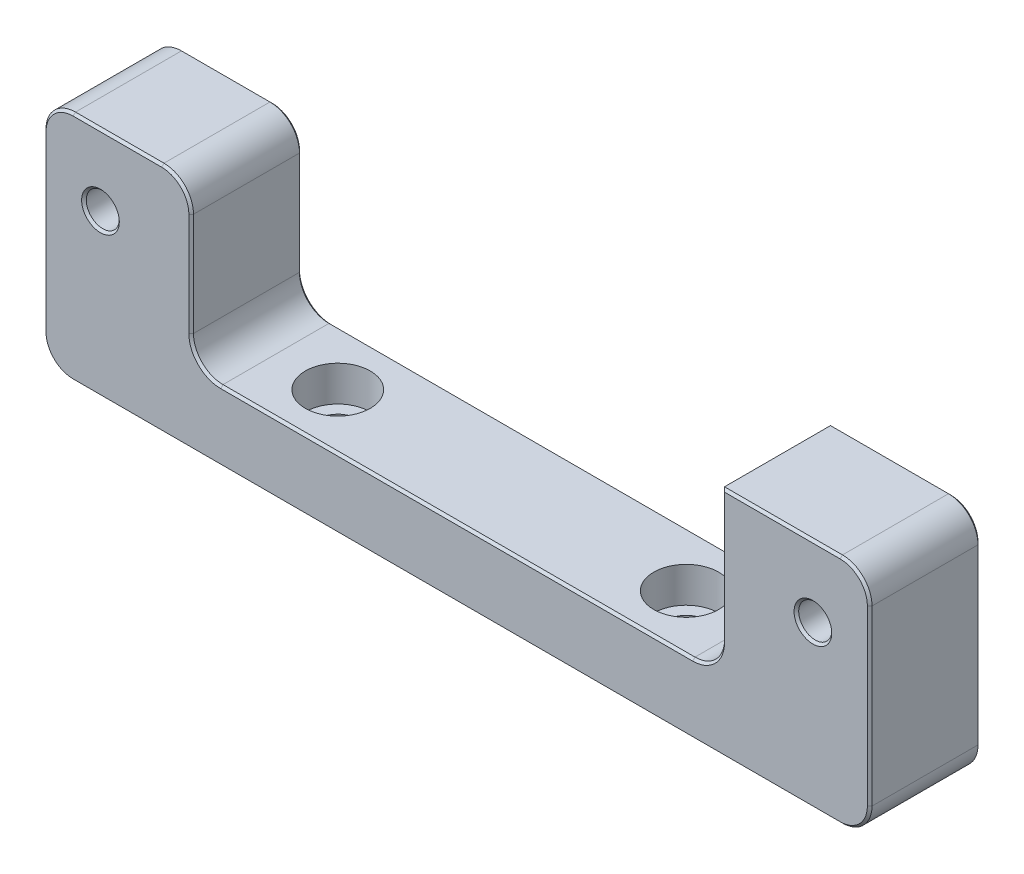
SolidWorks part; units mm, degrees
material "PEEK"
ref_plane "Front" through (0, 0, 0) normal (0, 0, 1) x (1, 0, 0)
ref_plane "Top" through (0, 0, 0) normal (0, 1, 0) x (1, 0, 0)
ref_plane "Right" through (0, 0, 0) normal (1, 0, 0) x (0, 0, -1)
sketch "Sketch1" plane through (0, 0, 0) normal (0, 0, 1) x (1, 0, 0)
  line L1 (0, 0) -> (-71.12, 0)
  line L2 (0, 0) -> (0, 20)
  line L3 (0, 20) -> (-71.12, 20)
  line L4 (-71.12, 0) -> (-71.12, 20)
  dimension "D1" = 71.12
  dimension "D2" = 20
extrude "Extrude1" add sketch "Sketch1" along normal blind 9.525
sketch "Sketch2" plane through (0, 0, 9.525) normal (0, 0, 1) x (1, 0, 0)
  line L0 (0, 20) -> (-71.12, 20) construction
  line L1 (-58.42, 20) -> (-12.7, 20)
  line L2 (-58.42, 20) -> (-58.42, 6.03)
  line L3 (-58.42, 6.03) -> (-12.7, 6.03)
  line L4 (-12.7, 20) -> (-12.7, 6.03)
  line L5 (0, 0) -> (0, 20) construction
  dimension "D1" = 13.97
  dimension "D2" = 45.72
  dimension "D3" = 12.7
extrude "Extrude2" cut sketch "Sketch2" against normal through all
ref_plane "Plane1" through (0, 0, 4.7625) normal (0, 0, -1) x (-1, 0, 0)
ref_plane "Plane2" through (-35.56, 0, 0) normal (-1, 0, 0) x (0, 0, 1)
hole_wizard "Hole1" positions "3DSketch1" profile "Sketch3" legacy end condition through all
sketch3d "3DSketch1"
  point P0 (-50.56, 6.03, 4.7625)
  point P2 (-20.56, 6.03, 4.7625)
  dimension "D1" = 15
  dimension "D2" = 15
sketch "Sketch3" plane through (-50.56, 6.03, 4.7625) normal (1, 0, 0) x (0, 0, 1)
  line L0 (0, 0) -> (0, 6.03)
  line L1 (0, 6.03) -> (1.7272, 6.03)
  line L3 (1.7272, 6.03) -> (1.7272, 3.048)
  line L4 (1.7272, 3.048) -> (2.794, 3.048)
  line L5 (2.794, 3.048) -> (2.794, 0)
  line L7 (2.794, 0) -> (0, 0)
  line L11 (0, -6.35) -> (0, 107.95) construction
  dimension "Thru Hole Dia." = 3.4544
  dimension "Thru Hole Depth" = 6.03
  dimension "C'Bore Dia." = 5.588
  dimension "C'Bore Depth" = 3.048
hole_wizard "#4-40 Tapped Hole1" positions "3DSketch2" profile "Sketch4" tap size "#4-40" standard "Ansi Inch"
sketch3d "3DSketch2"
  line L0 (-58.42, 20, 9.525) -> (-71.12, 20, 9.525) construction
  point P0 (-66.2305, 13.9, 9.525)
  point P2 (-4.8895, 13.9, 9.525)
  dimension "D1" = 6.1
  dimension "D2" = 30.6705
  dimension "D3" = 30.6705
sketch "Sketch4" plane through (-66.2305, 13.9, 9.525) normal (1, 0, 0) x (0, -1, 0)
  line L0 (0, 0) -> (0, 13.3538)
  line L1 (0, 13.3538) -> (1.1303, 12.6746)
  line L2 (1.1303, 12.6746) -> (1.1303, 10.7696)
  line L3 (1.1303, 10.7696) -> (1.4224, 10.7696)
  line L4 (1.4224, 10.7696) -> (1.4224, 0)
  line L5 (1.4224, 0) -> (0, 0)
  line L10 (0, 13.3538) -> (-1.1303, 12.6746) construction
  line L11 (0, -6.35) -> (0, 107.95) construction
  dimension "Tap Drill Dia." = 2.2606
  dimension "Tap Drill Depth" = 12.6746
  dimension "Thread Major Dia." = 2.8448
  dimension "Thread Depth" = 10.7696
  dimension "Drill Angle" = 118
fillet "Fillet1" radius 2.54 7 edges at (-71.12, 0, 4.7625) (-12.7, 6.03, 4.7625) (0, 0, 4.7625) (-58.42, 6.03, 4.7625) (-71.12, 20, 4.7625) (-58.42, 20, 4.7625) (0, 20, 4.7625)
chamfer "Chamfer1" distance 0.2 angle 45 34 edges at (-0.7439, 0.7439, 0) (0, 10, 0) (-0.7439, 19.2561, 0) (-7.62, 20, 0) (-12.7, 14.285, 0) (-13.4439, 6.7739, 0) (-35.56, 6.03, 0) (-57.6761, 6.7739, 0) (-58.42, 13.015, 0) (-59.1639, 19.2561, 0) (-64.77, 20, 0) (-70.3761, 19.2561, 0) (-71.12, 10, 0) (-70.3761, 0.7439, 0) (-35.56, 0, 0) (-3.4671, 13.9, 0) (-64.8081, 13.9, 0) (-70.3761, 19.2561, 9.525) (-64.77, 20, 9.525) (-59.1639, 19.2561, 9.525) (-58.42, 13.015, 9.525) (-57.6761, 6.7739, 9.525) (-35.56, 6.03, 9.525) (-13.4439, 6.7739, 9.525) (-12.7, 14.285, 9.525) (-7.62, 20, 9.525) (-0.7439, 19.2561, 9.525) (0, 10, 9.525) (-0.7439, 0.7439, 9.525) (-35.56, 0, 9.525) (-70.3761, 0.7439, 9.525) (-71.12, 10, 9.525) (-3.4671, 13.9, 9.525) (-64.8081, 13.9, 9.525)
equation "\"D3@3DSketch2\" = \"D2@3DSketch2\""
